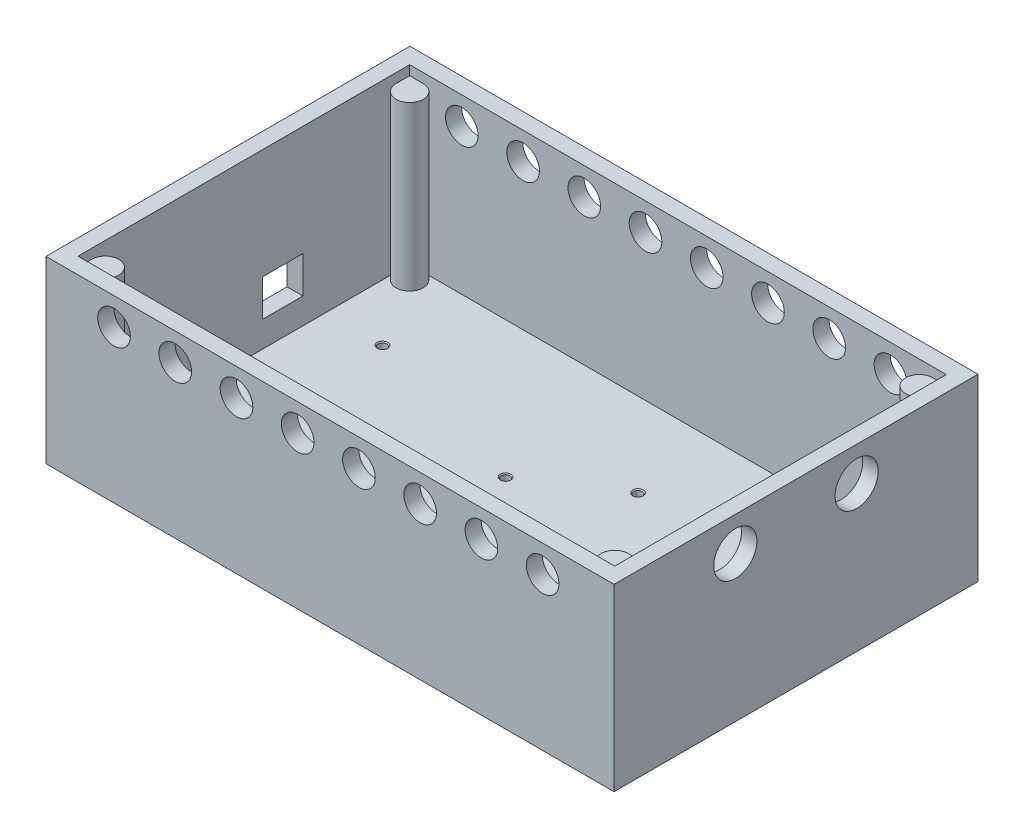
SolidWorks part; units mm, degrees
ref_plane "Front Plane" through (0, 0, 0) normal (0, 0, 1) x (1, 0, 0)
ref_plane "Top Plane" through (0, 0, 0) normal (0, 1, 0) x (1, 0, 0)
ref_plane "Right Plane" through (0, 0, 0) normal (1, 0, 0) x (0, 0, -1)
sketch "Sketch1" plane through (0, 0, 0) normal (0, 1, 0) x (1, 0, 0)
  line L1 (-96.1904, 42.7889) -> (70.8096, 42.7889)
  line L2 (-96.1904, 42.7889) -> (-96.1904, -64.2111)
  line L3 (-96.1904, -64.2111) -> (70.8096, -64.2111)
  line L4 (70.8096, 42.7889) -> (70.8096, -64.2111)
  dimension "D1" = 167
  dimension "D2" = 107
  dimension "D3" = 70.8096
  dimension "D4" = 42.7889
extrude "Boss-Extrude1" add sketch "Sketch1" along normal blind 52.8
sketch "Sketch2" plane through (0, 52.8, 0) normal (0, 1, 0) x (1, 0, 0)
  line L0 (-96.1904, 42.7889) -> (-96.1904, -64.2111) construction
  line L1 (-91.5404, 38.0389) -> (66.2596, 38.0389)
  line L2 (-91.5404, 38.0389) -> (-91.5404, -59.4611)
  line L3 (-91.5404, -59.4611) -> (66.2596, -59.4611)
  line L4 (66.2596, 38.0389) -> (66.2596, -59.4611)
  line L5 (70.8096, 42.7889) -> (-96.1904, 42.7889) construction
  dimension "D1" = 157.8
  dimension "D2" = 97.5
  dimension "D3" = 4.65
  dimension "D4" = 4.75
extrude "Cut-Extrude1" cut sketch "Sketch2" against normal blind 50.8
sketch "Sketch3" plane through (0, 0, 64.2111) normal (0, 0, 1) x (1, 0, 0)
  line L0 (-96.1904, 52.8) -> (70.8096, 52.8) construction
  line L1 (-96.1904, 52.8) -> (-96.1904, 0) construction
  circle A0 centre (-76.1904, 44.8) radius 4.8
  dimension "D1" = 9.6
  dimension "D2" = 8
  dimension "D3" = 20
extrude "Cut-Extrude2" cut sketch "Sketch3" against normal through all
pattern_linear "LPattern1" count 8 spacing 18 along (1, 0, 0) of "Cut-Extrude2"
sketch "Sketch4" plane through (70.8096, 0, 0) normal (1, 0, 0) x (0, 0, -1)
  line L0 (-64.2111, 52.8) -> (42.7889, 52.8) construction
  line L1 (-64.2111, 52.8) -> (-64.2111, 0) construction
  circle A0 centre (-28.5511, 42.8) radius 6.35
  dimension "D1" = 12.7
  dimension "D2" = 10
  dimension "D3" = 35.66
extrude "Cut-Extrude3" cut sketch "Sketch4" against normal up to next (4.55 mm away)
pattern_linear "LPattern2" count 2 spacing 35.66 along (0, 0, -1) of "Cut-Extrude3"
sketch "Sketch5" plane through (-96.1904, 0, 0) normal (-1, 0, 0) x (0, 0, 1)
  line L1 (-6.6689, 20.4) -> (5.2711, 20.4)
  line L2 (-6.6689, 20.4) -> (-6.6689, 9.6)
  line L3 (-6.6689, 9.6) -> (5.2711, 9.6)
  line L4 (5.2711, 20.4) -> (5.2711, 9.6)
  line L5 (-42.7889, 0) -> (64.2111, 0) construction
  line L6 (64.2111, 52.8) -> (64.2111, 0) construction
  dimension "D1" = 11.94
  dimension "D2" = 10.8
  dimension "D3" = 20.4
  dimension "D4" = 58.94
extrude "Cut-Extrude4" cut sketch "Sketch5" against normal up to next
sketch "Sketch6" plane through (0, 2, 0) normal (0, 1, 0) x (1, 0, 0)
  line L0 (66.2596, -59.4611) -> (66.2596, 38.0389) construction
  line L1 (66.2596, 38.0389) -> (-91.5404, 38.0389) construction
  line L2 (66.2596, -10.7111) -> (-91.5404, -10.7111) construction
  line L3 (-91.5404, 38.0389) -> (-91.5404, -59.4611) construction
  line L4 (-12.6404, -59.4611) -> (-12.6404, 38.0389) construction
  line L5 (-91.5404, -59.4611) -> (66.2596, -59.4611) construction
  line L6 (66.2596, 34.0389) -> (66.2596, 38.0389)
  line L7 (66.2596, 38.0389) -> (62.2596, 38.0389)
  line L8 (66.2596, -59.4611) -> (62.2596, -59.4611)
  line L9 (66.2596, -55.4611) -> (66.2596, -59.4611)
  line L10 (-91.5404, 38.0389) -> (-87.5404, 38.0389)
  line L11 (-91.5404, 34.0389) -> (-91.5404, 38.0389)
  line L12 (-91.5404, -55.4611) -> (-91.5404, -59.4611)
  line L13 (-91.5404, -59.4611) -> (-87.5404, -59.4611)
  arc A0 (62.2596, 38.0389) -> (66.2596, 34.0389) centre (62.2596, 34.0389) ccw
  arc A1 (62.2596, -59.4611) -> (66.2596, -55.4611) centre (62.2596, -55.4611) cw
  arc A2 (-87.5404, 38.0389) -> (-91.5404, 34.0389) centre (-87.5404, 34.0389) cw
  arc A3 (-87.5404, -59.4611) -> (-91.5404, -55.4611) centre (-87.5404, -55.4611) ccw
  dimension "D1" = 8
extrude "Boss-Extrude5" add sketch "Sketch6" along normal blind 48
hole_wizard "M3 Tapped Hole1" positions "Sketch7" profile "Sketch8" tap size "M3" standard "ISO" end condition through all
sketch "Sketch7" plane through (-49.0204, 2, -140.9448) normal (0, 1, 0) x (1, 0, 0)
  point P0 (56.7696, -175.8812)
  point P3 (25.7689, -171.0027)
  point P6 (-25.8566, -175.8812)
  point P9 (-25.8566, -127.545)
  point P12 (49.2766, -127.545)
  point P15 (25.7689, -142.9865)
sketch "Sketch8" plane through (7.7492, 2, 34.9363) normal (1, 0, 0) x (0, 0, 1)
  line L0 (0, 0) -> (0, 2)
  line L1 (0, 2) -> (1.25, 2)
  line L2 (1.25, 2) -> (1.25, 0.275)
  line L3 (1.25, 0.275) -> (1.525, 0)
  line L4 (1.525, 0) -> (0, 0)
  line L5 (-1.25, 0.275) -> (-1.525, 0) construction
  line L6 (0, -6.35) -> (0, 107.95) construction
  dimension "Thru Tap Drill Dia." = 2.5
  dimension "Thru Tap Drill Depth" = 2
  dimension "Near C'Sink Dia." = 3.05
  dimension "Near C'Sink Angle" = 90
cosmetic thread "Hole Thread1" parameters "D2"=3
cosmetic thread "Hole Thread2" parameters "D2"=3
cosmetic thread "Hole Thread3" parameters "D2"=3
cosmetic thread "Hole Thread4" parameters "D2"=3
cosmetic thread "Hole Thread5" parameters "D2"=3
cosmetic thread "Hole Thread6" parameters "D2"=3
